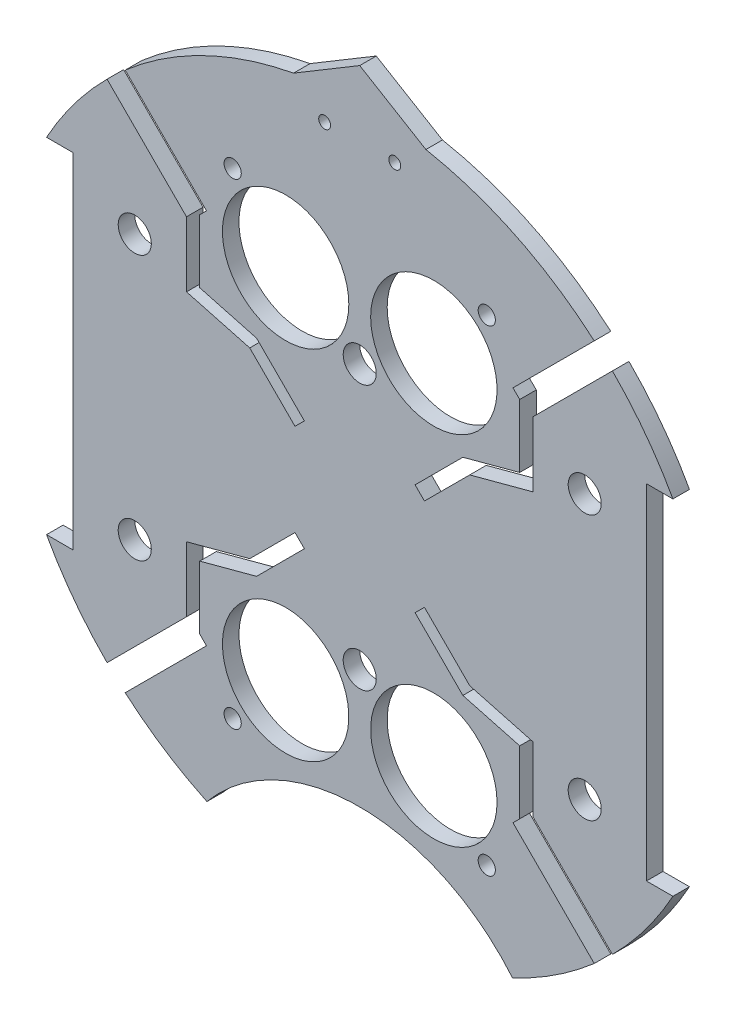
SolidWorks part; units mm, degrees
ref_plane "Front Plane" through (0, 0, 0) normal (0, 0, 1) x (1, 0, 0)
ref_plane "Top Plane" through (0, 0, 0) normal (0, 1, 0) x (1, 0, 0)
ref_plane "Right Plane" through (0, 0, 0) normal (1, 0, 0) x (0, 0, -1)
sketch "Sketch1" plane through (0, 0, 0) normal (0, 0, 1) x (1, 0, 0)
  line L0 (0, 0) -> (-82.1241, 0) construction
  line L1 (0, 0) -> (0, 95.6219) construction
  line L3 (-60.1074, 33.02) -> (-55.0274, 33.02)
  line L5 (-60.1074, -33.02) -> (-55.0274, -33.02)
  line L6 (-55.0274, 33.02) -> (-55.0274, -33.02)
  line L7 (60.1074, -33.02) -> (55.0274, -33.02)
  line L8 (60.1074, 33.02) -> (55.0274, 33.02)
  line L9 (55.0274, 33.02) -> (55.0274, -33.02)
  arc A0 (-60.1074, -33.02) -> (60.1074, -33.02) centre (0, 0) ccw
  circle A1 centre (-46.482, 10.795) radius 1.651 construction
  circle A2 centre (-21.082, 10.795) radius 1.651 construction
  circle A3 centre (-21.082, -10.795) radius 1.651 construction
  circle A4 centre (-46.482, -10.795) radius 1.651 construction
  circle A5 centre (46.482, -10.795) radius 1.651 construction
  circle A6 centre (21.082, -10.795) radius 1.651 construction
  circle A7 centre (21.082, 10.795) radius 1.651 construction
  circle A8 centre (46.482, 10.795) radius 1.651 construction
  arc A9 (60.1074, 33.02) -> (-60.1074, 33.02) centre (0, 0) ccw
  dimension "D2" = 3.302
  dimension "D3" = 3.302
  dimension "D4" = 25.4
  dimension "D5" = 10.795
  dimension "D10" = 46.482
  dimension "D12" = 10.795
  dimension "D6" = 66.04
  dimension "D7" = 5.08
  dimension "D8" = 68.58
  dimension "D9" = 68.58
  dimension "D11" = 33.02
extrude "Boss-Extrude2" add sketch "Sketch1" along normal blind 3.175
sketch "Sketch3" plane through (0, 0, 0) normal (0, 0, -1) x (-1, 0, 0)
  line L0 (0, 0) -> (0, -116.2908) construction
  line L1 (0, 0) -> (-153.8039, 0) construction
  line L2 (0, 0) -> (15.2681, -56.9814) construction
  circle A6 centre (14.224, -34.29) radius 12.1285
  circle A7 centre (14.224, 34.29) radius 12.1285
  circle A12 centre (-14.224, 34.29) radius 12.1285
  circle A13 centre (-14.224, -34.29) radius 12.1285
  point P36 (0, 0)
  point P53 (0, 0)
  point P55 (0, 0)
  dimension "D1" = 34.29
  dimension "D2" = 14.224
  dimension "D4" = 15
  dimension "D8" = 24.257
extrude "Cut-Extrude2" cut sketch "Sketch3" against normal through all
sketch "Sketch4" plane through (0, 0, 0) normal (0, 0, -1) x (-1, 0, 0)
  line L0 (0, 0) -> (0, -122.8047) construction
  line L1 (33.02, -67.2621) -> (-33.02, -67.2621)
  arc A0 (-60.1074, -33.02) -> (60.1074, -33.02) centre (0, 0) ccw construction
  circle A1 centre (0, -86.3121) radius 38.1
  dimension "D4" = 76.2
  dimension "D5" = 0
  dimension "D6" = 19.05
  dimension "D1" = 74.93
  dimension "D2" = 74.93
  dimension "D3" = 66.04
extrude "Cut-Extrude3" cut sketch "Sketch4" against normal through all
sketch "Sketch5" plane through (0, 0, 0) normal (0, 0, -1) x (-1, 0, 0)
  line L0 (19.7937, -19.7937) -> (10.6256, -10.6256)
  line L1 (-69.4248, 0) -> (69.4248, 0) construction
  line L2 (48.4934, -48.4934) -> (33.2448, -33.2448)
  line L3 (30.7048, -34.8511) -> (30.7048, -22.7173)
  line L4 (29.4103, -36.1455) -> (45.1258, -51.861)
  line L5 (45.1258, -51.861) -> (48.4934, -48.4934)
  line L6 (0, 0) -> (65.8076, -65.8076) construction
  line L7 (15.5824, -17.3784) -> (-2.7323, 0.9363) construction
  line L8 (33.2448, -33.2448) -> (33.2448, -20.7683)
  line L9 (21.1085, -17.5164) -> (-4.984, 8.5761) construction
  line L10 (30.7048, -22.7173) -> (19.7937, -19.7937)
  line L11 (12.4216, -8.8295) -> (21.1085, -17.5164)
  line L12 (33.2448, -20.7683) -> (21.1085, -17.5164)
  line L13 (0, 0) -> (46.9211, -12.5725) construction
  line L14 (29.4103, -36.1455) -> (30.7048, -34.8511)
  line L15 (-10.6256, -10.6256) -> (-10.7763, -10.7763)
  line L16 (12.4216, -8.8295) -> (10.6256, -10.6256)
  line L17 (10.6256, -10.6256) -> (10.7763, -10.7763)
  line L18 (0, 0) -> (-46.9211, -12.5725) construction
  line L19 (0, 0) -> (-65.8076, -65.8076) construction
  line L20 (-10.6256, -10.6256) -> (-10.7763, -10.7763)
  line L21 (-12.4216, -8.8295) -> (-10.6256, -10.6256)
  line L22 (-29.4103, -36.1455) -> (-30.7048, -34.8511)
  line L23 (-33.2448, -20.7683) -> (-21.1085, -17.5164)
  line L24 (-12.4216, -8.8295) -> (-21.1085, -17.5164)
  line L25 (-30.7048, -22.7173) -> (-19.7937, -19.7937)
  line L26 (-33.2448, -33.2448) -> (-33.2448, -20.7683)
  line L27 (-45.1258, -51.861) -> (-48.4934, -48.4934)
  line L28 (-29.4103, -36.1455) -> (-45.1258, -51.861)
  line L29 (-30.7048, -34.8511) -> (-30.7048, -22.7173)
  line L30 (0, 58.5122) -> (0, -56.1975) construction
  line L31 (-48.4934, -48.4934) -> (-33.2448, -33.2448)
  line L32 (-19.7937, -19.7937) -> (-10.6256, -10.6256)
  line L33 (-19.7937, 19.7937) -> (-10.6256, 10.6256)
  line L34 (-48.4934, 48.4934) -> (-33.2448, 33.2448)
  line L35 (-30.7048, 34.8511) -> (-30.7048, 22.7173)
  line L36 (-29.4103, 36.1455) -> (-45.1258, 51.861)
  line L37 (-45.1258, 51.861) -> (-48.4934, 48.4934)
  line L38 (-33.2448, 33.2448) -> (-33.2448, 20.7683)
  line L39 (-30.7048, 22.7173) -> (-19.7937, 19.7937)
  line L40 (-12.4216, 8.8295) -> (-21.1085, 17.5164)
  line L41 (-33.2448, 20.7683) -> (-21.1085, 17.5164)
  line L42 (-29.4103, 36.1455) -> (-30.7048, 34.8511)
  line L43 (-12.4216, 8.8295) -> (-10.6256, 10.6256)
  line L44 (-10.6256, 10.6256) -> (-10.7763, 10.7763)
  line L45 (10.6256, 10.6256) -> (10.7763, 10.7763)
  line L46 (12.4216, 8.8295) -> (10.6256, 10.6256)
  line L47 (-10.6256, 10.6256) -> (-10.7763, 10.7763)
  line L48 (29.4103, 36.1455) -> (30.7048, 34.8511)
  line L49 (33.2448, 20.7683) -> (21.1085, 17.5164)
  line L50 (12.4216, 8.8295) -> (21.1085, 17.5164)
  line L51 (30.7048, 22.7173) -> (19.7937, 19.7937)
  line L52 (33.2448, 33.2448) -> (33.2448, 20.7683)
  line L53 (45.1258, 51.861) -> (48.4934, 48.4934)
  line L54 (29.4103, 36.1455) -> (45.1258, 51.861)
  line L55 (30.7048, 34.8511) -> (30.7048, 22.7173)
  line L56 (48.4934, 48.4934) -> (33.2448, 33.2448)
  line L57 (19.7937, 19.7937) -> (10.6256, 10.6256)
  circle A0 centre (0, 0) radius 15.24 construction
  arc A1 (29.3285, -61.9924) -> (60.1074, -33.02) centre (0, 0) ccw construction
  dimension "D7" = 2.54
  dimension "D8" = 2.54
  dimension "D6" = 30.48
  dimension "D5" = 1.27
  dimension "D1" = 45
  dimension "D2" = 4.7625
  dimension "D3" = 22.225
  dimension "D4" = 0
  dimension "D9" = 15
  dimension "D10" = 2.54
extrude "Cut-Extrude6" cut sketch "Sketch5" against normal through all
sketch "Sketch9" plane through (0, 0, 0) normal (0, 0, -1) x (-1, 0, 0)
  line L0 (12.7, 67.3938) -> (0, 75)
  line L1 (0, 75) -> (-12.7, 67.3938)
  arc A2 (12.7, 67.3938) -> (-12.7, 67.3938) centre (0, 0) ccw
extrude "Boss-Extrude3" add sketch "Sketch9" against normal blind 3.175
extrude "Cut-Extrude7" cut sketch "Sketch10" against normal through all
sketch "Sketch10" plane through (-31.3134, 132.559, 6.35) normal (0, 0, 1) x (0, 1, 0)
  line L0 (-132.559, -31.3134) -> (-245.9178, -31.3134) construction
  line L1 (-132.559, -31.3134) -> (-132.559, -129.4011) construction
  circle A0 centre (-180.819, -4.6434) radius 1.651
  circle A3 centre (-180.819, -57.9834) radius 1.651
  circle A4 centre (-84.299, -57.9834) radius 1.651
  circle A5 centre (-84.299, -4.6434) radius 1.651
extrude "Cut-Extrude8" cut sketch "Sketch11" against normal through all both and the other way through all
sketch "Sketch11" plane through (-31.3134, 132.614, 38.1) normal (0, 0, 1) x (0, 1, 0)
  line L0 (-132.614, -31.3134) -> (-132.614, 57.8454) construction
  line L1 (-132.614, -31.3134) -> (-222.516, -31.3134) construction
  circle A0 centre (-158.014, 14.4066) radius 3.175
  circle A1 centre (-173.254, -31.3134) radius 3.175
  circle A3 centre (-158.014, -77.0334) radius 3.175
  circle A4 centre (-107.214, -77.0334) radius 3.175
  circle A5 centre (-91.974, -31.3134) radius 3.175
  circle A6 centre (-107.214, 14.4066) radius 3.175
sketch "Sketch12" plane through (0, 0, 0) normal (0, 0, -1) x (-1, 0, 0)
  line L0 (0, -13.969) -> (0, 24.0636) construction
  circle A0 centre (6.731, 62.23) radius 1.143
  circle A1 centre (-6.731, 62.23) radius 1.143
  dimension "D1" = 2.286
  dimension "D2" = 62.23
  dimension "D3" = 6.731
extrude "Cut-Extrude9" cut sketch "Sketch12" against normal through all
extrude "Cut-Extrude10" cut sketch "Sketch13" against normal blind 55.88
sketch "Sketch13" plane through (30.092, 4.0835, 15.875) normal (0, 0, 1) x (1, 0, 0)
  line L0 (-30.092, -4.0835) -> (54.8907, -4.0835) construction
  line L2 (-30.092, -4.0835) -> (-30.092, 87.8604) construction
  circle A0 centre (-54.476, -49.8035) radius 1.651
  circle A2 centre (-54.476, 41.6365) radius 1.651
  circle A3 centre (-5.708, -49.8035) radius 1.651
  circle A4 centre (-5.708, 41.6365) radius 1.651
extrude "Cut-Extrude11" cut sketch "Sketch14" against normal through all
sketch "Sketch14" plane through (30.092, 4.0835, -53.975) normal (0, 0, -1) x (-1, 0, 0)
  line L0 (30.092, -4.0835) -> (148.6336, -4.0835) construction
  line L1 (30.092, -4.0835) -> (30.092, 90.452) construction
  circle A0 centre (-13.088, 21.3165) radius 3.175
  circle A1 centre (73.272, 21.3165) radius 3.175
  circle A2 centre (30.092, 21.3165) radius 3.175
  circle A4 centre (73.272, -29.4835) radius 3.175
  circle A5 centre (30.092, -29.4835) radius 3.175
  circle A6 centre (-13.088, -29.4835) radius 3.175
